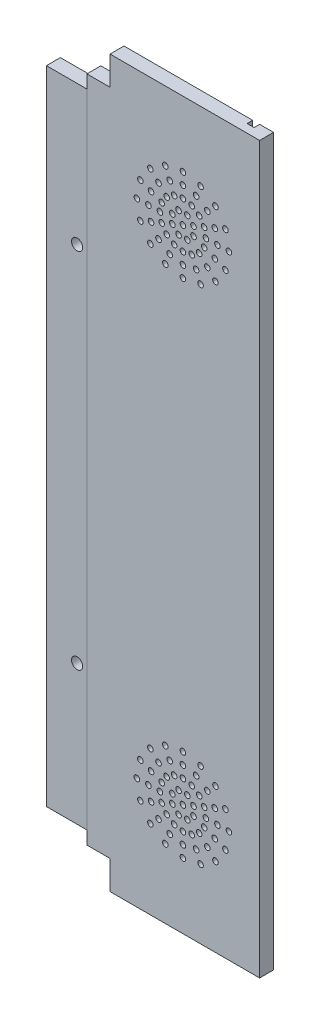
SolidWorks part; units mm, degrees
ref_plane "Alzado" through (0, 0, 0) normal (0, 0, 1) x (1, 0, 0)
ref_plane "Planta" through (0, 0, 0) normal (0, 1, 0) x (1, 0, 0)
ref_plane "Vista lateral" through (0, 0, 0) normal (1, 0, 0) x (0, 0, -1)
sketch "Croquis1" plane through (0, 0, 0) normal (0, 0, 1) x (1, 0, 0)
  line L0 (-35.8039, 125.1863) -> (32.117, 125.1863)
  line L1 (-35.8039, 125.1863) -> (-35.8039, -134.8137)
  line L2 (-35.8039, -134.8137) -> (32.117, -134.8137)
  line L3 (32.117, 125.1863) -> (32.117, -134.8137)
  dimension "D1" = 260
  dimension "D2" = 67.9209
extrude "Saliente-Extruir1" add sketch "Croquis1" along normal blind 5
sketch "Croquis2" [suppressed] plane through (0, 0, 5) normal (0, 0, 1) x (1, 0, 0)
  line L0 (32.117, -4.8137) -> (27.117, -4.8137) construction
  line L1 (32.117, -134.8137) -> (32.117, 125.1863) construction
  line L2 (-35.8039, -134.8137) -> (32.117, -134.8137) construction
  line L3 (27.117, -134.8137) -> (24.617, -134.8137)
  line L4 (27.117, -134.8137) -> (27.117, 125.1863)
  line L5 (27.117, 125.1863) -> (24.617, 125.1863)
  line L6 (24.617, -134.8137) -> (24.617, 125.1863)
  line L7 (32.117, 125.1863) -> (-35.8039, 125.1863) construction
  dimension "D1" = 5
  dimension "D2" = 2.5
extrude "Cortar-Extruir1" [suppressed] cut sketch "Croquis2" against normal blind 2
sketch "Croquis3" plane through (0, 0, 0) normal (0, 0, -1) x (-1, 0, 0)
  line L2 (35.8039, -134.8137) -> (-32.117, -134.8137) construction
  line L3 (-27.117, -134.8137) -> (-24.617, -134.8137)
  line L4 (-27.117, -134.8137) -> (-27.117, 125.1863)
  line L5 (-27.117, 125.1863) -> (-24.617, 125.1863)
  line L6 (-24.617, -134.8137) -> (-24.617, 125.1863)
  line L7 (-32.117, 125.1863) -> (35.8039, 125.1863) construction
  line L8 (-32.117, -4.8137) -> (-27.117, -4.8137) construction
  line L9 (-32.117, -134.8137) -> (-32.117, 125.1863) construction
  dimension "D1" = 2.5
  dimension "D3" = 5
extrude "Cortar-Extruir2" cut sketch "Croquis3" against normal blind 2
sketch "Croquis4" plane through (0, 0, 0) normal (0, 0, -1) x (-1, 0, 0)
  line L0 (35.8039, -134.8137) -> (-24.617, -134.8137) construction
  line L1 (35.8039, 125.1863) -> (29.8039, 125.1863)
  line L2 (35.8039, 125.1863) -> (35.8039, -134.8137)
  line L3 (35.8039, -134.8137) -> (29.8039, -134.8137)
  line L4 (29.8039, 114.8863) -> (29.8039, -124.5137)
  line L5 (29.8039, 125.1863) -> (21.5039, 125.1863)
  line L6 (21.5039, 125.1863) -> (21.5039, 114.8863)
  line L7 (21.5039, 114.8863) -> (29.8039, 114.8863)
  line L8 (29.8039, -134.8137) -> (21.5039, -134.8137)
  line L9 (21.5039, -134.8137) -> (21.5039, -124.5137)
  line L10 (21.5039, -124.5137) -> (29.8039, -124.5137)
  dimension "D1" = 6
extrude "Cortar-Extruir3" cut sketch "Croquis4" against normal up to next
sketch "Croquis5" plane through (0, 0, 0) normal (0, 0, -1) x (-1, 0, 0)
  line L0 (-32.117, -4.8137) -> (29.8039, -4.8137) construction
  line L1 (-32.117, -134.8137) -> (-32.117, 125.1863) construction
  line L2 (-4.617, -134.8137) -> (-4.617, 125.1863)
  line L3 (-4.617, -134.8137) -> (-4.617, 125.1863) construction
  line L4 (29.8039, 114.8863) -> (29.8039, -124.5137) construction
  circle A0 centre (-4.617, 85.1863) radius 17.5 construction
  circle A1 centre (-4.617, -94.8137) radius 17.5 construction
  circle A2 centre (-4.617, 101.6863) radius 1
  circle A3 centre (-4.617, 97.5563) radius 1
  circle A4 centre (-4.617, 93.4263) radius 1
  circle A6 centre (-4.617, 85.1663) radius 1
  circle A7 centre (-3.0442, 88.9835) radius 1
  circle A8 centre (-1.4637, 92.7991) radius 1
  circle A9 centre (0.1168, 96.6147) radius 1
  circle A10 centre (1.6973, 100.4303) radius 1
  circle A12 centre (1.2095, 91.0129) radius 1
  circle A13 centre (4.1299, 93.9332) radius 1
  circle A14 centre (7.0502, 96.8536) radius 1
  circle A15 centre (-0.8199, 86.7592) radius 1
  circle A16 centre (2.9958, 88.3396) radius 1
  circle A17 centre (6.8114, 89.9201) radius 1
  circle A18 centre (10.627, 91.5006) radius 1
  circle A20 centre (3.623, 85.1863) radius 1
  circle A21 centre (7.753, 85.1863) radius 1
  circle A22 centre (11.883, 85.1863) radius 1
  circle A23 centre (-0.8199, 83.6135) radius 1
  circle A24 centre (2.9958, 82.033) radius 1
  circle A25 centre (6.8114, 80.4525) radius 1
  circle A26 centre (10.627, 78.872) radius 1
  circle A28 centre (1.2095, 79.3598) radius 1
  circle A29 centre (4.1299, 76.4394) radius 1
  circle A30 centre (7.0502, 73.5191) radius 1
  circle A31 centre (-3.0442, 81.3892) radius 1
  circle A32 centre (-1.4637, 77.5736) radius 1
  circle A33 centre (0.1168, 73.7579) radius 1
  circle A34 centre (1.6973, 69.9423) radius 1
  circle A36 centre (-4.617, 76.9463) radius 1
  circle A37 centre (-4.617, 72.8163) radius 1
  circle A38 centre (-4.617, 68.6863) radius 1
  circle A39 centre (-6.1898, 81.3892) radius 1
  circle A40 centre (-7.7703, 77.5736) radius 1
  circle A41 centre (-9.3508, 73.7579) radius 1
  circle A42 centre (-10.9313, 69.9423) radius 1
  circle A44 centre (-10.4436, 79.3598) radius 1
  circle A45 centre (-13.3639, 76.4394) radius 1
  circle A46 centre (-16.2843, 73.5191) radius 1
  circle A47 centre (-8.4142, 83.6135) radius 1
  circle A48 centre (-12.2298, 82.033) radius 1
  circle A49 centre (-16.0454, 80.4525) radius 1
  circle A50 centre (-19.861, 78.872) radius 1
  circle A52 centre (-12.857, 85.1863) radius 1
  circle A53 centre (-16.987, 85.1863) radius 1
  circle A54 centre (-21.117, 85.1863) radius 1
  circle A55 centre (-8.4142, 86.7592) radius 1
  circle A56 centre (-12.2298, 88.3396) radius 1
  circle A57 centre (-16.0454, 89.9201) radius 1
  circle A58 centre (-19.861, 91.5006) radius 1
  circle A60 centre (-10.4436, 91.0129) radius 1
  circle A61 centre (-13.3639, 93.9332) radius 1
  circle A62 centre (-16.2843, 96.8536) radius 1
  circle A63 centre (-6.1898, 88.9835) radius 1
  circle A64 centre (-7.7703, 92.7991) radius 1
  circle A65 centre (-9.3508, 96.6147) radius 1
  circle A66 centre (-10.9313, 100.4303) radius 1
  circle A74 centre (-4.617, 89.2963) radius 1 [skipped]
  circle A75 centre (-10.9313, -110.0577) radius 1
  circle A76 centre (-9.3508, -106.2421) radius 1
  circle A77 centre (-7.7703, -102.4264) radius 1
  circle A78 centre (-6.1898, -98.6108) radius 1
  circle A79 centre (-16.2843, -106.4809) radius 1
  circle A80 centre (-13.3639, -103.5606) radius 1
  circle A81 centre (-10.4436, -100.6402) radius 1
  circle A82 centre (-19.861, -101.128) radius 1
  circle A83 centre (-16.0454, -99.5475) radius 1
  circle A84 centre (-12.2298, -97.967) radius 1
  circle A85 centre (-8.4142, -96.3865) radius 1
  circle A86 centre (-21.117, -94.8137) radius 1
  circle A87 centre (-16.987, -94.8137) radius 1
  circle A88 centre (-12.857, -94.8137) radius 1
  circle A89 centre (-19.861, -88.4994) radius 1
  circle A90 centre (-16.0454, -90.0799) radius 1
  circle A91 centre (-12.2298, -91.6604) radius 1
  circle A92 centre (-8.4142, -93.2408) radius 1
  circle A93 centre (-16.2843, -83.1464) radius 1
  circle A94 centre (-13.3639, -86.0668) radius 1
  circle A95 centre (-10.4436, -88.9871) radius 1
  circle A96 centre (-10.9313, -79.5697) radius 1
  circle A97 centre (-9.3508, -83.3853) radius 1
  circle A98 centre (-7.7703, -87.2009) radius 1
  circle A99 centre (-6.1898, -91.0165) radius 1
  circle A100 centre (-4.617, -78.3137) radius 1
  circle A101 centre (-4.617, -82.4437) radius 1
  circle A102 centre (-4.617, -86.5737) radius 1
  circle A103 centre (1.6973, -79.5697) radius 1
  circle A104 centre (0.1168, -83.3853) radius 1
  circle A105 centre (-1.4637, -87.2009) radius 1
  circle A106 centre (-3.0442, -91.0165) radius 1
  circle A107 centre (7.0502, -83.1464) radius 1
  circle A108 centre (4.1299, -86.0668) radius 1
  circle A109 centre (1.2095, -88.9871) radius 1
  circle A110 centre (10.627, -88.4994) radius 1
  circle A111 centre (6.8114, -90.0799) radius 1
  circle A112 centre (2.9958, -91.6604) radius 1
  circle A113 centre (-0.8199, -93.2408) radius 1
  circle A114 centre (11.883, -94.8137) radius 1
  circle A115 centre (7.753, -94.8137) radius 1
  circle A116 centre (3.623, -94.8137) radius 1
  circle A117 centre (10.627, -101.128) radius 1
  circle A118 centre (6.8114, -99.5475) radius 1
  circle A119 centre (2.9958, -97.967) radius 1
  circle A120 centre (-0.8199, -96.3865) radius 1
  circle A121 centre (7.0502, -106.4809) radius 1
  circle A122 centre (4.1299, -103.5606) radius 1
  circle A123 centre (1.2095, -100.6402) radius 1
  circle A124 centre (1.6973, -110.0577) radius 1
  circle A125 centre (0.1168, -106.2421) radius 1
  circle A126 centre (-1.4637, -102.4264) radius 1
  circle A127 centre (-3.0442, -98.6108) radius 1
  circle A128 centre (-4.617, -94.7937) radius 1
  circle A129 centre (-4.617, -103.0537) radius 1
  circle A130 centre (-4.617, -107.1837) radius 1
  circle A131 centre (-4.617, -111.3137) radius 1
  point P145 (-4.617, 85.1863)
  dimension "D2" = 35
  dimension "D4" = 5
  dimension "D3" = 180
  dimension "D1" = 20
  dimension "D5" = 16
extrude "Cortar-Extruir4" cut sketch "Croquis5" against normal up to next (5 mm away)
sketch "Croquis6" plane through (0, 0, 0) normal (0, 0, -1) x (-1, 0, 0)
  line L1 (29.8139, 110.1863) -> (29.8139, -119.8137)
  line L2 (44.3139, 114.8863) -> (44.3139, -124.5137)
  line L3 (44.3139, 110.1863) -> (44.3139, -119.8137)
  line L4 (29.8139, 110.1863) -> (44.3139, 110.1863)
  line L5 (29.8139, -119.8137) -> (44.3139, -119.8137)
  line L6 (-32.117, -4.8137) -> (44.3039, -4.8137) construction
  line L7 (-32.117, -134.8137) -> (-32.117, 125.1863) construction
  circle A0 centre (33.3139, 60.1863) radius 2
  circle A1 centre (33.3139, -69.8137) radius 2
  dimension "D2" = 4
  dimension "D3" = 130
  dimension "D4" = 11
  dimension "D5" = 230
  dimension "D1" = 14.51
extrude "Saliente-Extruir2" add sketch "Croquis6" against normal up to vertex (5 mm away)
sketch "Croquis7" [suppressed] plane through (0, 0, 0) normal (0, 0, -1) x (-1, 0, 0)
  line L0 (35.8039, -134.8137) -> (-32.117, -134.8137) construction
  line L1 (35.8039, 125.1863) -> (25.8039, 125.1863)
  line L2 (35.8039, 125.1863) -> (35.8039, -134.8137)
  line L3 (35.8039, -134.8137) -> (25.8039, -134.8137)
  line L4 (25.8039, 125.1863) -> (25.8039, -134.8137)
  dimension "D1" = 10
extrude "Cortar-Extruir5" [suppressed] cut sketch "Croquis7" against normal up to next
